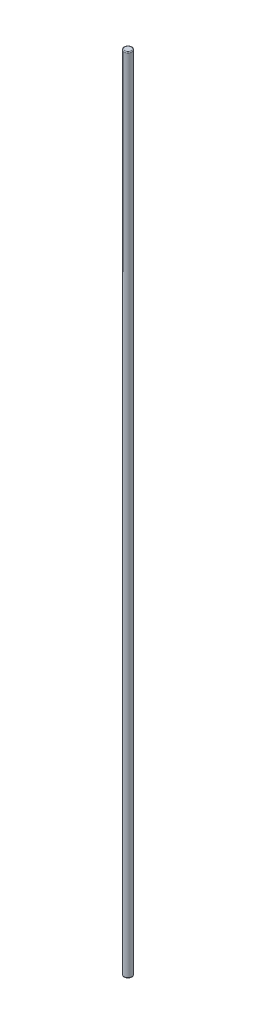
SolidWorks part; units mm, degrees
ref_plane "Front Plane" through (0, 0, 0) normal (0, 0, 1) x (1, 0, 0)
ref_plane "Top Plane" through (0, 0, 0) normal (0, 1, 0) x (1, 0, 0)
ref_plane "Right Plane" through (0, 0, 0) normal (1, 0, 0) x (0, 0, -1)
sketch "Sketch1" plane through (0, 0, 0) normal (0, 1, 0) x (1, 0, 0)
  circle A0 centre (0, 0) radius 1
  dimension "D1" = 2
extrude "Boss-Extrude1" add sketch "Sketch1" along normal blind 200
fillet "Fillet1" radius 0.2 2 edges at (0, 200, 1) (0, 0, 1)
